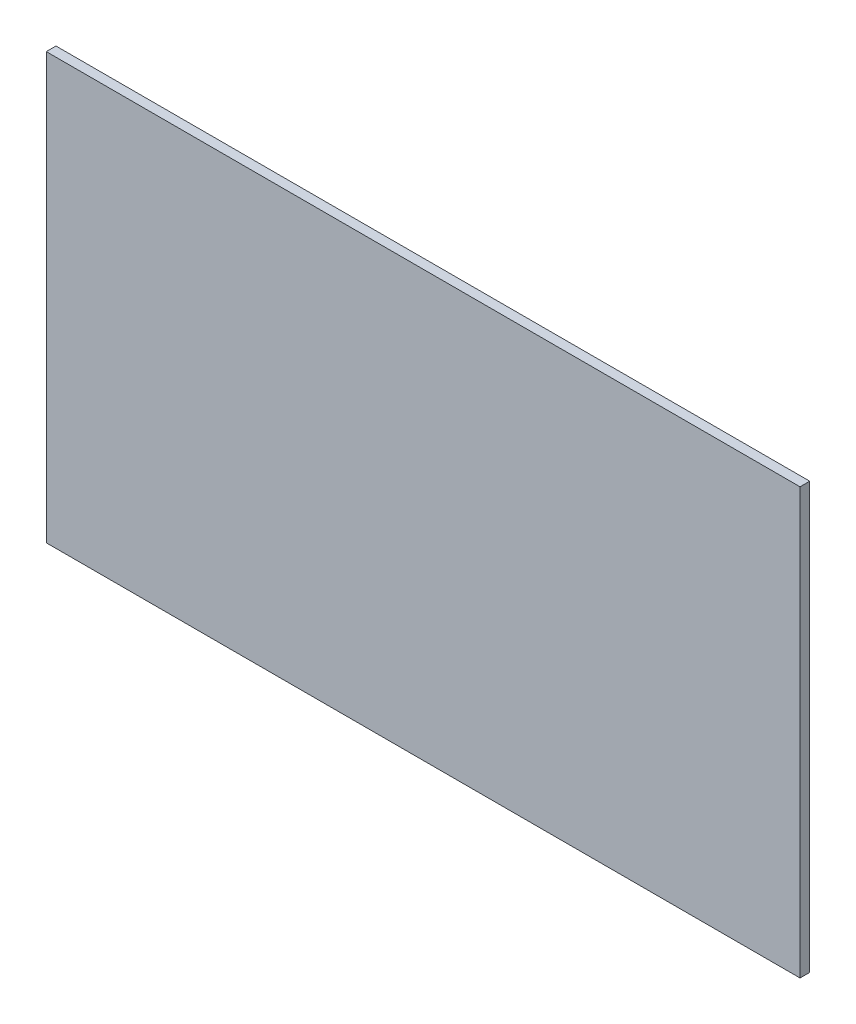
SolidWorks part; units mm, degrees
ref_plane "Front Plane" through (0, 0, 0) normal (0, 0, 1) x (1, 0, 0)
ref_plane "Top Plane" through (0, 0, 0) normal (0, 1, 0) x (1, 0, 0)
ref_plane "Right Plane" through (0, 0, 0) normal (1, 0, 0) x (0, 0, -1)
sketch "Sketch2" plane through (0, 0, 0) normal (0, 0, 1) x (1, 0, 0)
  line L0 (108, -131.5) -> (233, -131.5) construction
  line L1 (0, 0) -> (233, 0)
  line L2 (0, 0) -> (0, -131.5)
  line L3 (0, -131.5) -> (233, -131.5)
  line L4 (233, 0) -> (233, -131.5)
  dimension "D1" = 233
extrude "Boss-Extrude1" add sketch "Sketch2" along normal blind 3
